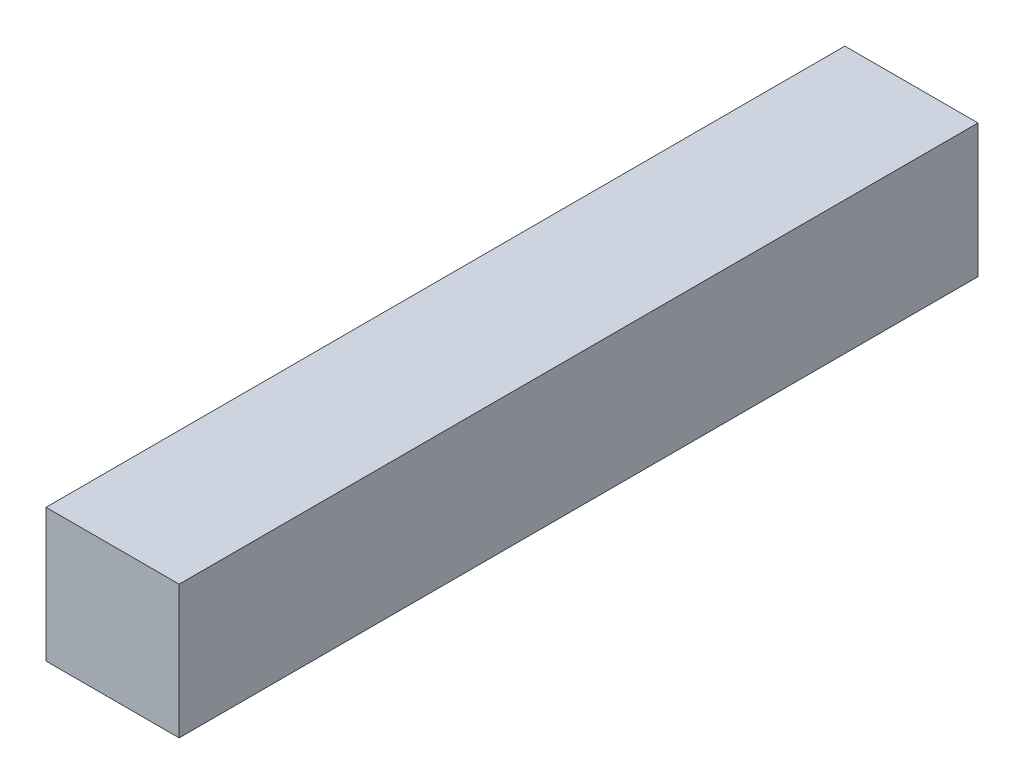
SolidWorks part; units mm, degrees
material "6061 Alloy"
ref_plane "Front Plane" through (0, 0, 0) normal (0, 0, 1) x (1, 0, 0)
ref_plane "Top Plane" through (0, 0, 0) normal (0, 1, 0) x (1, 0, 0)
ref_plane "Right Plane" through (0, 0, 0) normal (1, 0, 0) x (0, 0, -1)
sketch "Sketch1" plane through (0, 0, 0) normal (0, 0, 1) x (1, 0, 0)
  line L1 (0, 0) -> (12.7, 0)
  line L2 (0, 0) -> (0, -12.7)
  line L3 (0, -12.7) -> (12.7, -12.7)
  line L4 (12.7, 0) -> (12.7, -12.7)
  dimension "D1" = 12.7
  dimension "D2" = 12.7
extrude "Boss-Extrude1" add sketch "Sketch1" along normal blind 76.2
sketch "Sketch2" plane through (0, 0, 0) normal (0, 1, 0) x (1, 0, 0)
  line L0 (12.7, 0) -> (0, 0) construction
  line L1 (6.35, 0) -> (6.35, -7.6954) construction
  point P0 (6.35, 0)
